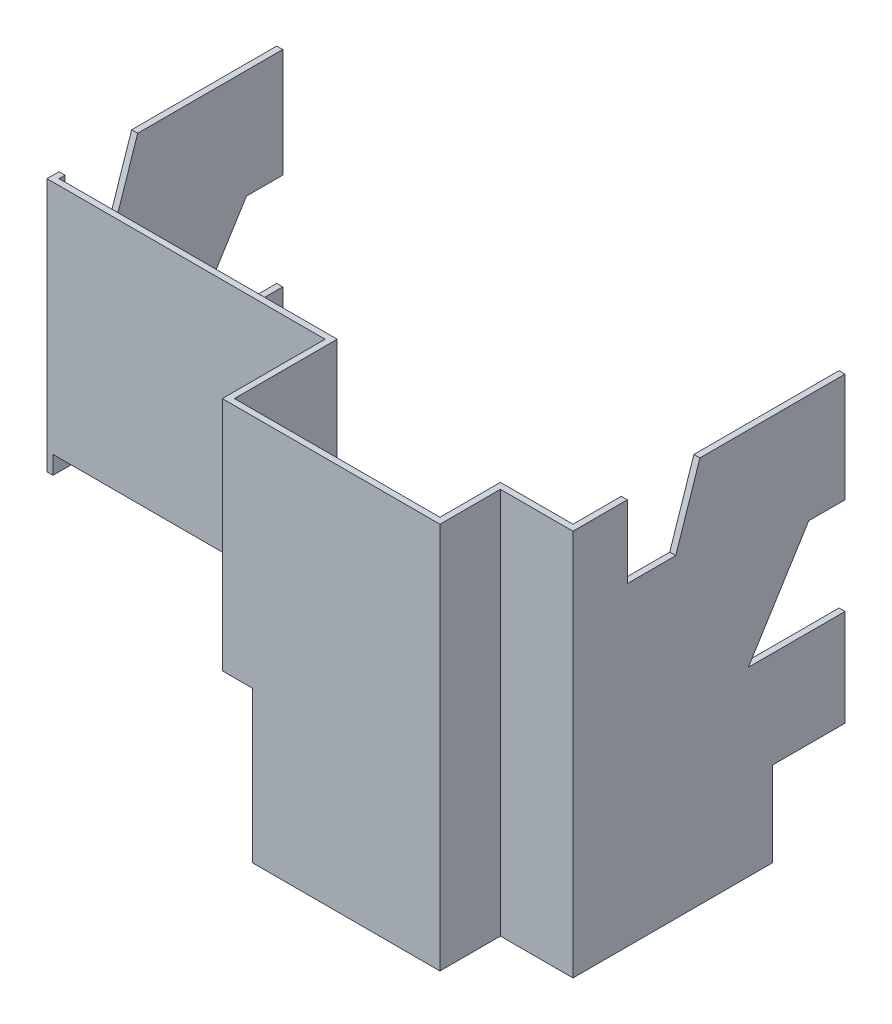
SolidWorks part; units mm, degrees
ref_plane "Front Plane" through (0, 0, 0) normal (0, 0, 1) x (1, 0, 0)
ref_plane "Top Plane" through (0, 0, 0) normal (0, 1, 0) x (1, 0, 0)
ref_plane "Right Plane" through (0, 0, 0) normal (1, 0, 0) x (0, 0, -1)
sketch "Sketch1" plane through (0, 0, 0) normal (0, 1, 0) x (1, 0, 0)
  line L0 (0, 0) -> (0, 241.3)
  line L1 (0, 241.3) -> (6.35, 241.3)
  line L2 (6.35, 241.3) -> (6.35, 6.35)
  line L3 (6.35, 6.35) -> (298.45, 6.35)
  line L4 (0, 0) -> (292.1, 0)
  line L5 (292.1, 0) -> (292.1, -107.95)
  line L6 (292.1, -107.95) -> (520.7, -107.95)
  line L8 (520.7, -44.45) -> (596.9, -44.45)
  line L9 (596.9, -44.45) -> (596.9, 241.3)
  line L10 (596.9, 241.3) -> (590.55, 241.3)
  line L11 (590.55, 241.3) -> (590.55, -38.1)
  line L12 (590.55, -38.1) -> (514.35, -38.1)
  line L14 (514.35, -101.6) -> (298.45, -101.6)
  line L15 (298.45, -101.6) -> (298.45, 6.35)
  line L16 (514.35, -38.1) -> (514.35, -101.6)
  line L17 (520.7, -107.95) -> (520.7, -44.45)
  dimension "D1" = 241.3
  dimension "D2" = 6.35
  dimension "D3" = 6.35
  dimension "D4" = 6.35
  dimension "D5" = 6.35
  dimension "D6" = 6.35
  dimension "D7" = 6.35
  dimension "D8" = 6.35
  dimension "D9" = 596.9
  dimension "D10" = 228.6
  dimension "D11" = 76.2
  dimension "D12" = 90
  dimension "D13" = 107.95
  dimension "D14" = 6.35
  dimension "D15" = 63.5
extrude "Boss-Extrude1" add sketch "Sketch1" along normal blind 406.4
sketch "Sketch2" plane through (0, 0, 107.95) normal (0, 0, 1) x (1, 0, 0)
  line L0 (292.1, 0) -> (520.7, 0) construction
  line L2 (323.85, 0) -> (323.85, 158.75)
  line L3 (323.85, 158.75) -> (6.35, 158.75)
  line L5 (6.35, 406.4) -> (6.35, 0) construction
  line L6 (323.85, 0) -> (6.35, 0)
  line L11 (6.35, 0) -> (6.35, 158.75)
  point P6 (6.35, 158.75)
  point P7 (0, 0)
  point P8 (-97.7577, 0)
  point P9 (327.0466, 0)
  dimension "D1" = 158.75
  dimension "D2" = 317.5
extrude "Cut-Extrude1" cut sketch "Sketch2" against normal up to surface (114.3 mm away) up to face at (152.4, 203.2, -6.35)
sketch "Sketch3" plane through (0, 0, 0) normal (-1, 0, 0) x (0, 0, 1)
  line L0 (0, 406.4) -> (0, 0) construction
  line L2 (-76.2, 88.9) -> (-76.2, 139.7)
  line L3 (-76.2, 139.7) -> (0, 139.7)
  line L4 (0, 0) -> (0, 139.7)
  line L6 (-241.3, 0) -> (0, 0)
  line L7 (-241.3, 0) -> (-241.3, 88.9)
  line L8 (-241.3, 88.9) -> (-76.2, 88.9)
  point P10 (300.7721, 0)
  point P12 (4.5715, 0)
  dimension "D1" = 88.9
  dimension "D2" = 50.8
  dimension "D3" = 76.2
extrude "Cut-Extrude2" cut sketch "Sketch3" against normal up to next
sketch "Sketch4" plane through (596.9, 0, 0) normal (1, 0, 0) x (0, 0, -1)
  line L1 (241.3, 0) -> (165.1, 0)
  line L2 (241.3, 0) -> (241.3, 88.9)
  line L3 (241.3, 88.9) -> (165.1, 88.9)
  line L4 (165.1, 0) -> (165.1, 88.9)
  dimension "D1" = 88.9
  dimension "D2" = 76.2
extrude "Cut-Extrude3" cut sketch "Sketch4" against normal up to next
sketch "Sketch6" plane through (0, 0, 0) normal (-1, 0, 0) x (0, 0, 1)
  line L0 (-241.3, 406.4) -> (-241.3, 88.9) construction
  line L1 (-241.3, 292.1) -> (-203.2, 292.1)
  line L2 (-241.3, 292.1) -> (-241.3, 190.5)
  line L3 (-241.3, 190.5) -> (-139.7, 190.5)
  line L4 (-203.2, 292.1) -> (-139.7, 190.5)
  line L5 (-241.3, 406.4) -> (0, 406.4) construction
  line L6 (-88.9, 406.4) -> (-12.7, 406.4)
  line L7 (-88.9, 406.4) -> (-63.5, 330.2)
  line L8 (-63.5, 330.2) -> (-12.7, 330.2)
  line L9 (-12.7, 406.4) -> (-12.7, 330.2)
  point P12 (-95.3074, 406.4)
  point P13 (-161.0067, 191.8975)
  point P14 (-139.9738, 191.7471)
  point P15 (-202.2015, 292.1)
  point P16 (-203.7286, 292.1)
  point P17 (-197.6203, 292.1)
  dimension "D1" = 114.3
  dimension "D2" = 101.6
  dimension "D3" = 38.1
  dimension "D4" = 152.4
  dimension "D5" = 50.8
  dimension "D6" = 76.2
  dimension "D7" = 101.6
  dimension "D8" = 76.2
extrude "Cut-Extrude5" cut sketch "Sketch6" against normal through all
